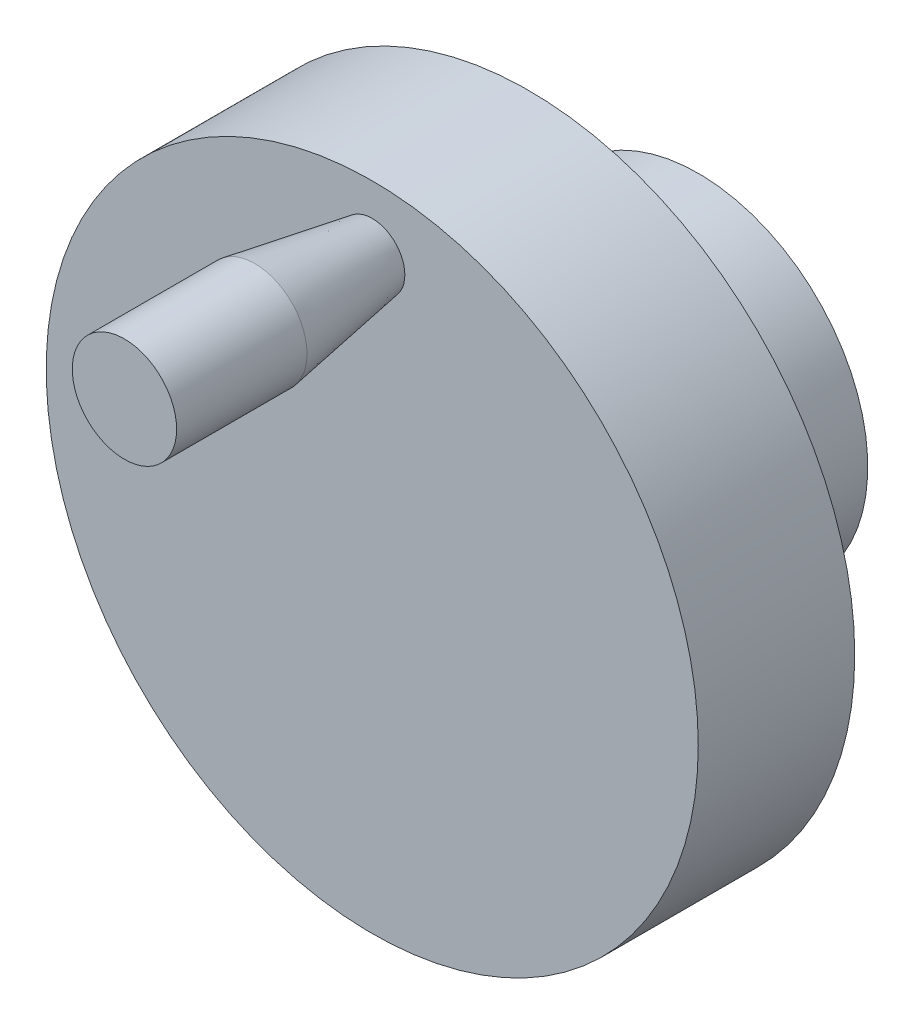
SolidWorks part; units mm, degrees
ref_plane "前视基准面" through (0, 0, 0) normal (0, 0, 1) x (1, 0, 0)
ref_plane "上视基准面" through (0, 0, 0) normal (0, 1, 0) x (1, 0, 0)
ref_plane "右视基准面" through (0, 0, 0) normal (1, 0, 0) x (0, 0, -1)
sketch "草图1" plane through (0, 0, 0) normal (0, 0, 1) x (1, 0, 0)
  circle A0 centre (0, 0) radius 25
  dimension "D1" = 50
extrude "凸台-拉伸1" add sketch "草图1" along normal blind 12
sketch "草图2" plane through (0, 0, 0) normal (0, 0, -1) x (-1, 0, 0)
  circle A0 centre (0, 0) radius 13
  dimension "D1" = 26
extrude "凸台-拉伸2" add sketch "草图2" along normal blind 13
sketch "草图3" plane through (0, 0, -13) normal (0, 0, -1) x (-1, 0, 0)
  circle A0 centre (0, 0) radius 4
  dimension "D1" = 8
extrude "切除-拉伸1" cut sketch "草图3" against normal up to surface (13 mm away) up to face at (-13, 0, 0)
sketch "草图4" plane through (0, 0, 0) normal (1, 0, 0) x (0, 0, -1)
  line L0 (-12, 22.5) -> (-21, 24)
  line L2 (-21, 24) -> (-31, 24)
  line L3 (-31, 24) -> (-31, 20)
  line L6 (-12, 20) -> (-12, 22.5)
  line L7 (-31, 20) -> (-12, 20)
  line L8 (-12, 25) -> (-12, -25) construction
  dimension "D1" = 20
  dimension "D2" = 19
  dimension "D3" = 10
  dimension "D4" = 4
  dimension "D5" = 2.5
revolve "旋转1" add sketch "草图4" angle 360 about L7
